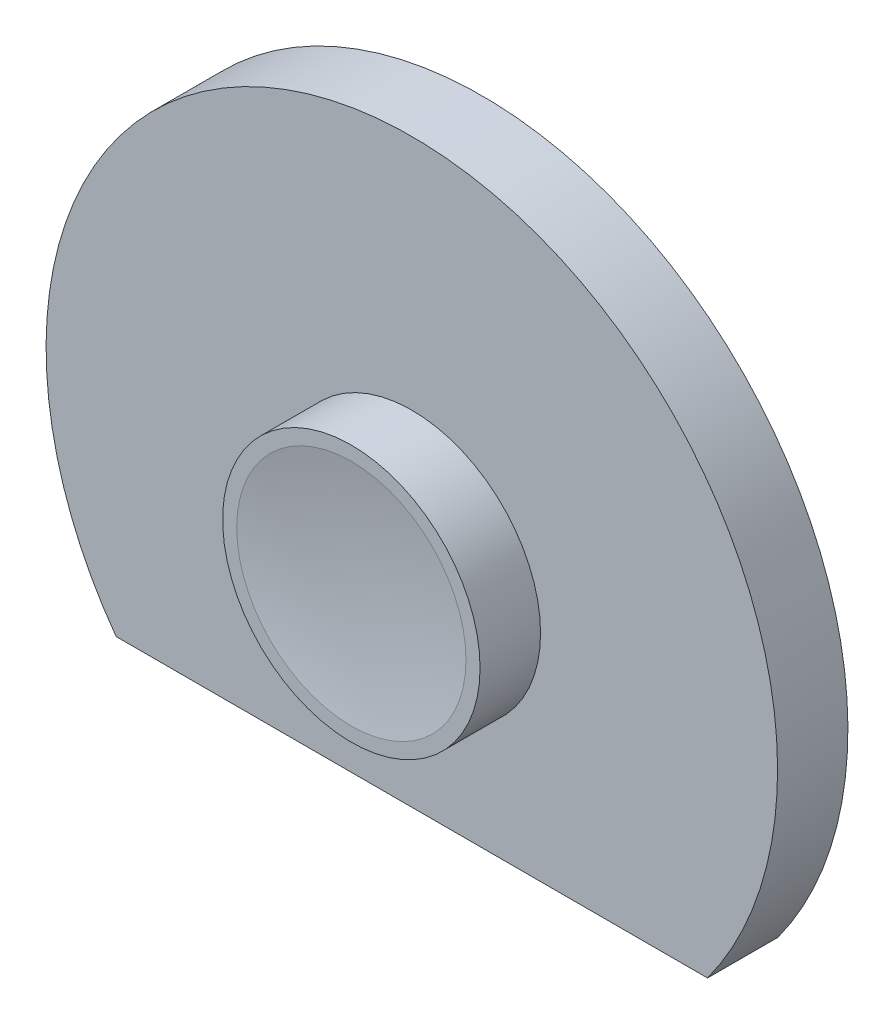
SolidWorks part; units mm, degrees
ref_plane "Front Plane" through (0, 0, 0) normal (0, 0, 1) x (1, 0, 0)
ref_plane "Top Plane" through (0, 0, 0) normal (0, 1, 0) x (1, 0, 0)
ref_plane "Right Plane" through (0, 0, 0) normal (1, 0, 0) x (0, 0, -1)
sketch "Sketch1" plane through (0, 0, 0) normal (0, 0, 1) x (1, 0, 0)
  line L0 (-21.0217, -15.3) -> (21.0217, -15.3)
  arc A0 (21.0217, -15.3) -> (-21.0217, -15.3) centre (0, 0) ccw
  point P6 (0, 26)
  dimension "D1" = 52
  dimension "D2" = 41.3
extrude "Boss-Extrude1" add sketch "Sketch1" along normal blind 5
sketch "Sketch2" plane through (0, 0, 5) normal (0, 0, 1) x (1, 0, 0)
  circle A0 centre (0, 0) radius 9.15
  dimension "D1" = 18.3
extrude "Boss-Extrude2" add sketch "Sketch2" along normal blind 4.3
sketch "Sketch3" plane through (0, 0, 0) normal (0, -1, 0) x (1, 0, 0)
  line L0 (0, 9.3) -> (0, 8.6313)
  line L1 (9.15, 9.3) -> (-9.15, 9.3) construction
  line L2 (8.15, 9.3) -> (0, 9.3)
  arc A0 (0, 8.6313) -> (8.15, 9.3) centre (0, 58.6313) ccw
  point P8 (0, 0)
  point P9 (9.15, 9.3)
  point P10 (0, 0)
  point P11 (8.6252, 9.3)
  dimension "D1" = 50
  dimension "D2" = 1
revolve "Cut-Revolve1" cut sketch "Sketch3" angle 360 about L0
